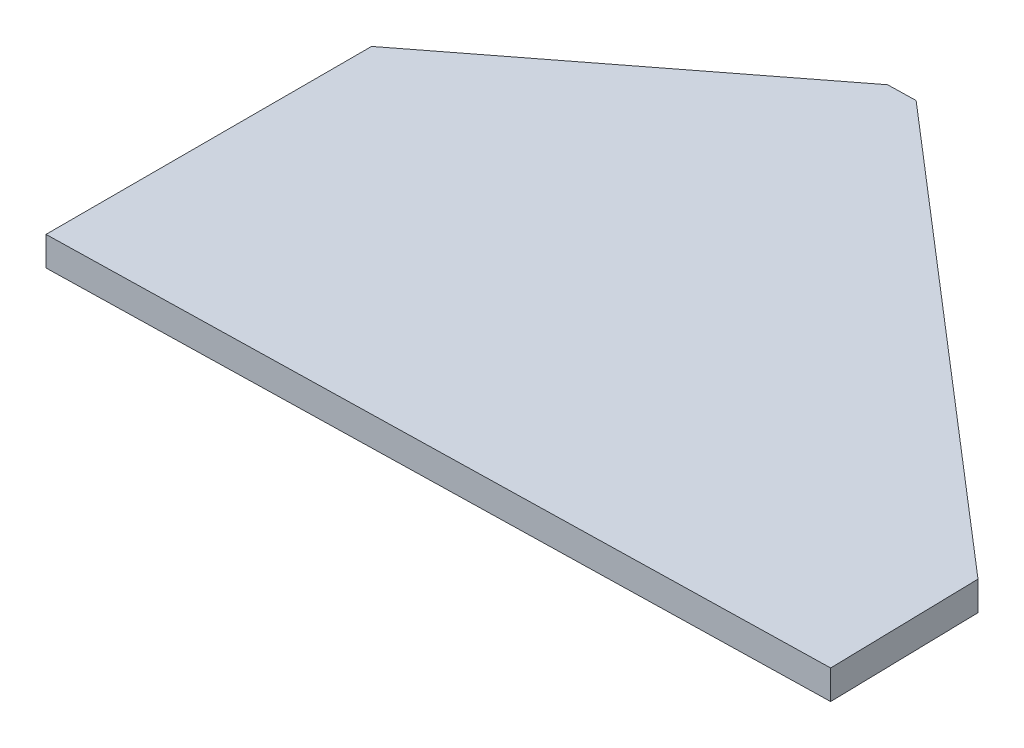
SolidWorks part; units mm, degrees
ref_plane "Plan de face" through (0, 0, 0) normal (0, 0, 1) x (1, 0, 0)
ref_plane "Plan de dessus" through (0, 0, 0) normal (0, 1, 0) x (1, 0, 0)
ref_plane "Plan de droite" through (0, 0, 0) normal (1, 0, 0) x (0, 0, -1)
sketch "Esquisse1" plane through (0, 0, 0) normal (0, 1, 0) x (1, 0, 0)
  line L3 (0, 22.3553) -> (0, 0)
  line L4 (0, 0) -> (52.7263, 1.156)
  line L5 (52.7263, 1.156) -> (52.4995, 11.4999)
  line L6 (52.4995, 11.4999) -> (21.9149, 37.8358)
  line L7 (21.9149, 37.8358) -> (19.9952, 37.7937)
  line L8 (19.9952, 37.7937) -> (0, 22.3553)
  point P6 (0, 0)
extrude "Boss.-Extru.1" add sketch "Esquisse1" along normal blind 2
